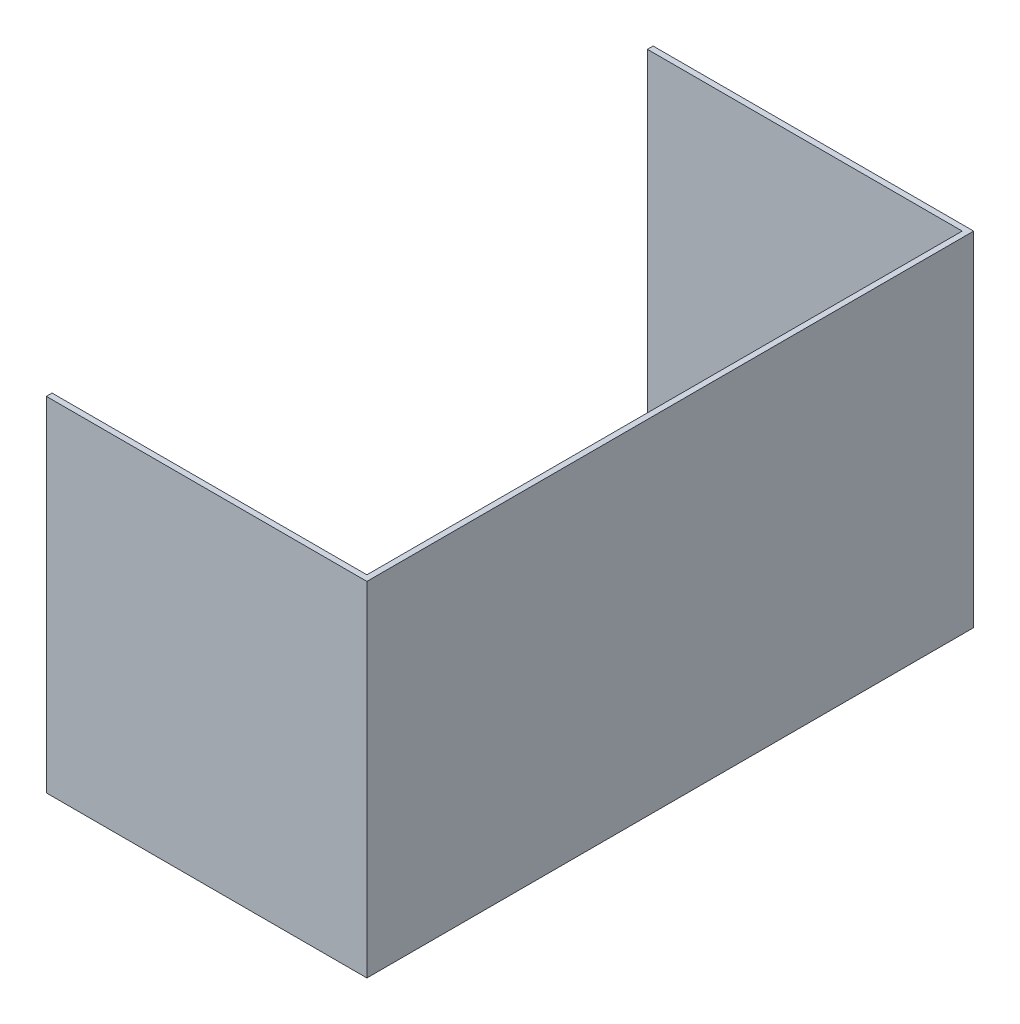
SolidWorks part; units mm, degrees
ref_plane "Front Plane" through (0, 0, 0) normal (0, 0, 1) x (1, 0, 0)
ref_plane "Top Plane" through (0, 0, 0) normal (0, 1, 0) x (1, 0, 0)
ref_plane "Right Plane" through (0, 0, 0) normal (1, 0, 0) x (0, 0, -1)
sketch "Sketch1" plane through (0, 0, 0) normal (0, 1, 0) x (1, 0, 0)
  line L0 (-6.35, 666.75) -> (-355.6, 666.75)
  line L1 (0, 0) -> (-355.6, 0)
  line L2 (0, 0) -> (0, 673.1)
  line L3 (0, 673.1) -> (-355.6, 673.1)
  line L4 (-355.6, 0) -> (-355.6, 6.35)
  line L5 (-6.35, 6.35) -> (-6.35, 666.75)
  line L6 (-6.35, 6.35) -> (-355.6, 6.35)
  line L7 (-355.6, 666.75) -> (-355.6, 673.1)
  dimension "D1" = 6.35
  dimension "D2" = 355.6
  dimension "D3" = 673.1
extrude "Boss-Extrude1" add sketch "Sketch1" along normal blind 381
